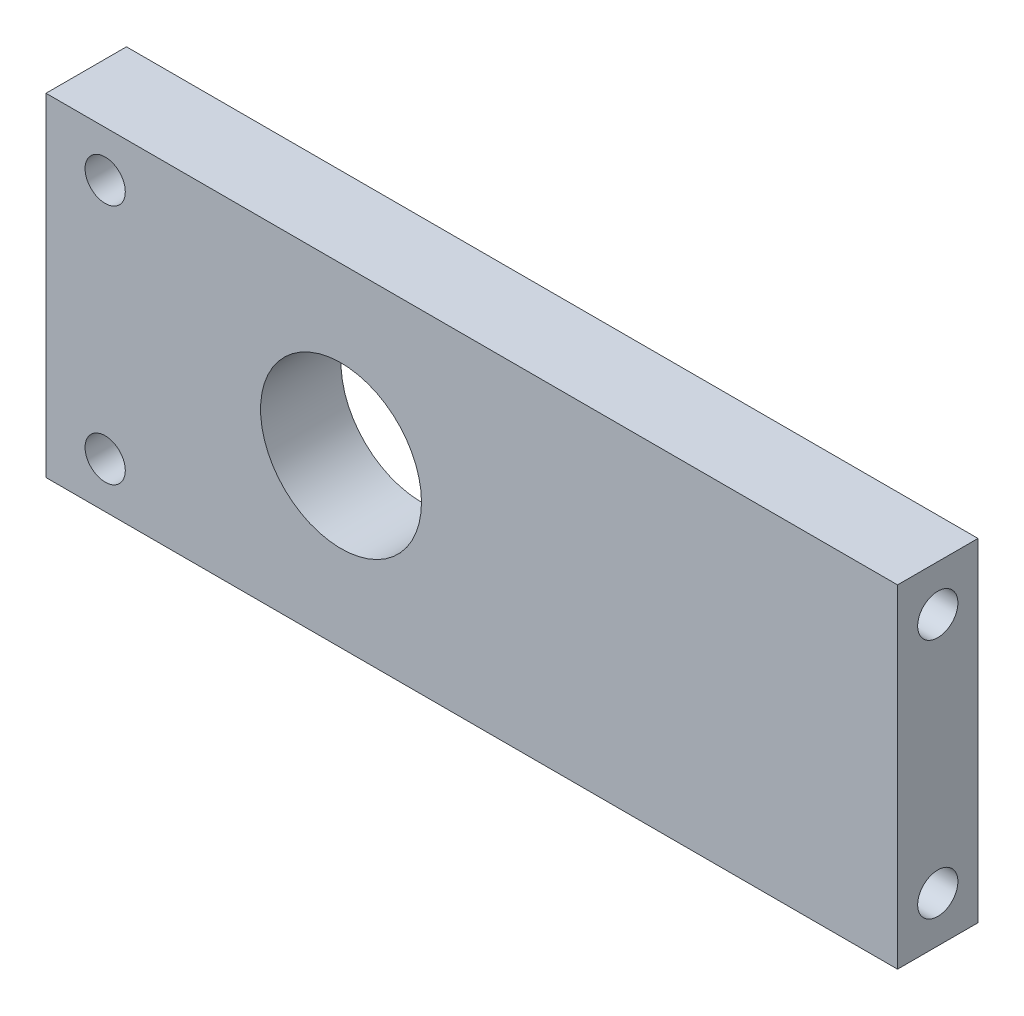
SolidWorks part; units mm, degrees
ref_plane "Plan de face" through (0, 0, 0) normal (0, 0, 1) x (1, 0, 0)
ref_plane "Plan de dessus" through (0, 0, 0) normal (0, 1, 0) x (1, 0, 0)
ref_plane "Plan de droite" through (0, 0, 0) normal (1, 0, 0) x (0, 0, -1)
sketch "Esquisse1" plane through (0, 0, 0) normal (0, 0, 1) x (1, 0, 0)
  line L1 (-18.4451, 11.0077) -> (45.0549, 11.0077)
  line L2 (-18.4451, 11.0077) -> (-18.4451, -13.8123)
  line L3 (-18.4451, -13.8123) -> (45.0549, -13.8123)
  line L4 (45.0549, 11.0077) -> (45.0549, -13.8123)
  circle A0 centre (3.5549, -1.4023) radius 6
  dimension "D5" = 12
  dimension "D1" = 24.82
  dimension "D2" = 63.5
  dimension "D3" = 22
  dimension "D4" = 12.41
extrude "Boss.-Extru.1" add sketch "Esquisse1" along normal blind 6
sketch "Esquisse2" plane through (45.0549, 0, 0) normal (1, 0, 0) x (0, 0, -1)
  line L0 (-6, -13.8123) -> (-6, 11.0077) construction
  line L1 (-6, 11.0077) -> (0, 11.0077) construction
  line L2 (-6, -13.8123) -> (0, -13.8123) construction
  circle A0 centre (-3, 7.5977) radius 1.5
  circle A1 centre (-3, -10.4023) radius 1.5
  dimension "D1" = 3
  dimension "D2" = 3
  dimension "D3" = 3
  dimension "D4" = 3
  dimension "D5" = 3.41
  dimension "D6" = 3.41
extrude "Enlèv. mat.-Extru.1" cut sketch "Esquisse2" against normal blind 10
sketch "Esquisse3" plane through (0, 0, 0) normal (0, 0, -1) x (-1, 0, 0)
  line L0 (-45.0549, 11.0077) -> (18.4451, 11.0077) construction
  line L1 (18.4451, -13.8123) -> (-45.0549, -13.8123) construction
  circle A0 centre (14.0319, 7.5977) radius 1.5
  circle A1 centre (14.0319, -10.4023) radius 1.5
  dimension "D1" = 3
  dimension "D2" = 3
  dimension "D3" = 3.41
  dimension "D4" = 3.41
extrude "Enlèv. mat.-Extru.2" cut sketch "Esquisse3" against normal blind 10
